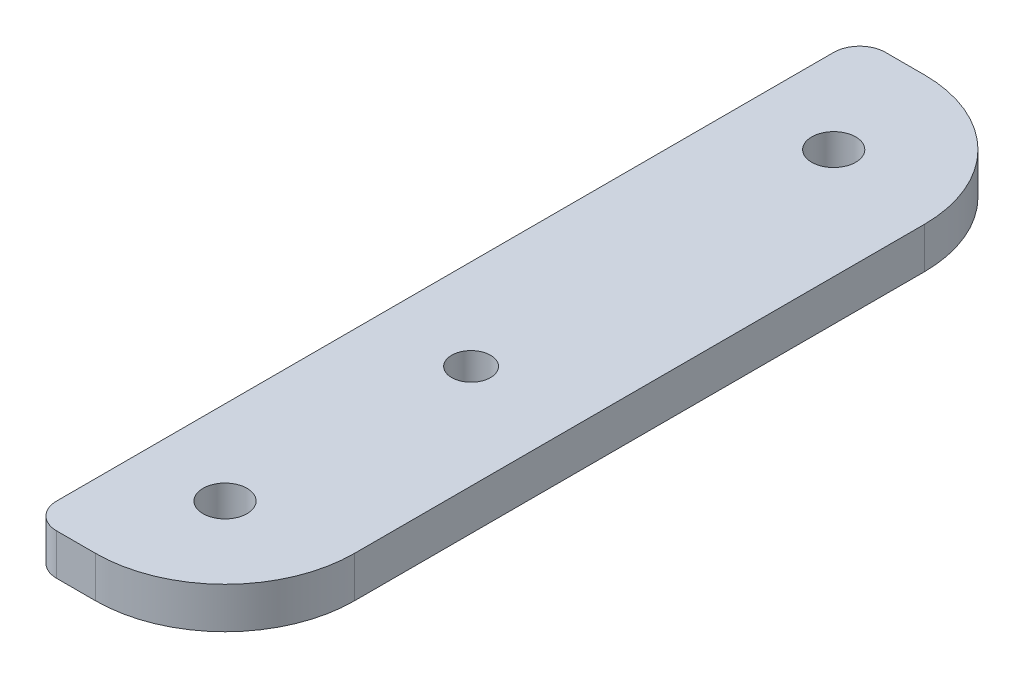
SolidWorks part; units mm, degrees
ref_plane "Front Plane" through (0, 0, 0) normal (0, 0, 1) x (1, 0, 0)
ref_plane "Top Plane" through (0, 0, 0) normal (0, 1, 0) x (1, 0, 0)
ref_plane "Right Plane" through (0, 0, 0) normal (1, 0, 0) x (0, 0, -1)
sketch "Sketch1" plane through (0, 0, 0) normal (0, 1, 0) x (1, 0, 0)
  line L0 (-32, 32) -> (32, -32) construction
  line L1 (-22, 32) -> (22, 32)
  line L2 (-32, 22) -> (-32, -22)
  line L3 (-22, -32) -> (22, -32)
  line L4 (32, 22) -> (32, -22)
  arc A0 (-32, -22) -> (-22, -32) centre (-22, -22) ccw
  arc A1 (22, -32) -> (32, -22) centre (22, -22) ccw
  arc A2 (22, 32) -> (32, 22) centre (22, 22) cw
  arc A3 (-32, 22) -> (-22, 32) centre (-22, 22) cw
  point P12 (32, 32)
  dimension "D2" = 10
  dimension "D1" = 64
extrude "Boss-Extrude2" add sketch "Sketch1" along normal blind 3.175 contours L2 A0 L3 A1 L4 A2 L1 A3
sketch "Sketch3" plane through (0, 3.175, 0) normal (0, 1, 0) x (1, 0, 0)
  line L0 (23.5, 23.5) -> (-23.5, -23.5) construction
  line L1 (-23.5, 23.5) -> (23.5, -23.5) construction
  circle A0 centre (-23.5, 23.5) radius 1.7
  circle A1 centre (23.5, 23.5) radius 1.7
  circle A2 centre (23.5, -23.5) radius 1.7
  circle A3 centre (-23.5, -23.5) radius 1.7
  point P8 (23.3506, -20.8543)
  point P9 (0, 0)
  point P13 (0, 0)
  dimension "D1" = 3.4
  dimension "D2" = 47
  dimension "D3" = 47
extrude "Cut-Extrude2" cut sketch "Sketch3" against normal blind 3.175
sketch "Sketch4" plane through (0, 3.175, 0) normal (0, 1, 0) x (1, 0, 0)
  line L0 (-24, -5) -> (24, -5) construction
  line L1 (0, 0) -> (0, -11.8827) construction
  circle A0 centre (24, -5) radius 1.5
  circle A1 centre (-24, -5) radius 1.5
  point P4 (0, 0)
  dimension "D1" = 3
  dimension "D2" = 48
  dimension "D3" = 5
extrude "Cut-Extrude3" cut sketch "Sketch4" against normal blind 3.175
sketch "Sketch5" plane through (0, 3.175, 0) normal (0, 1, 0) x (1, 0, 0)
  line L0 (-22, -32) -> (22, -32) construction
  line L1 (17, -32) -> (-44.7651, -32)
  line L2 (17, -32) -> (17, 32)
  line L3 (17, 32) -> (-44.7651, 32)
  line L4 (-44.7651, -32) -> (-44.7651, 32)
  line L5 (-22, 32) -> (22, 32) construction
  line L6 (32, 22) -> (32, -22) construction
  dimension "D1" = 15
extrude "Cut-Extrude4" cut sketch "Sketch5" against normal blind 3.175
fillet "Fillet1" radius 2 2 edges at (17, 1.5875, 32) (17, 1.5875, -32)
